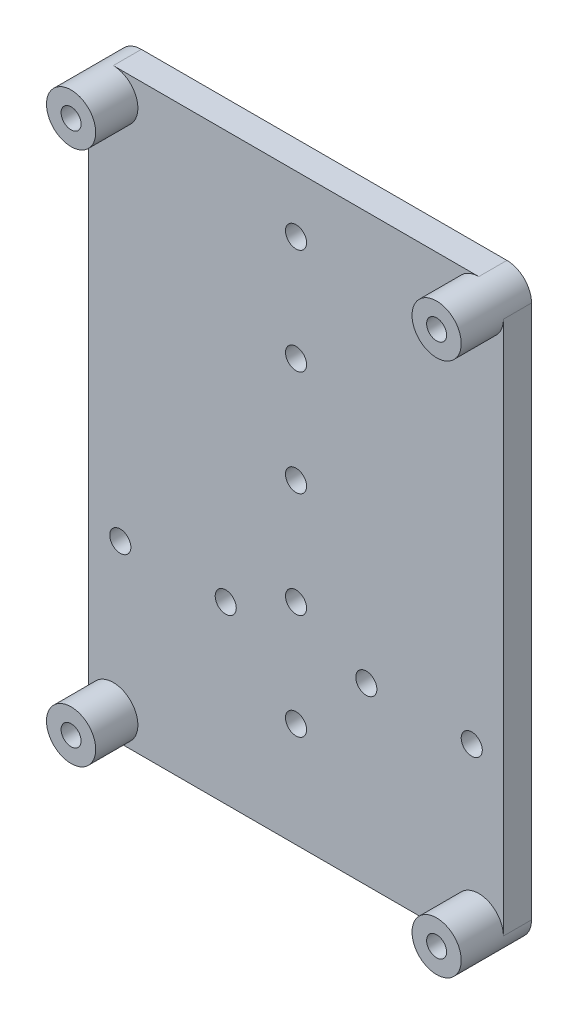
SolidWorks part; units mm, degrees
ref_plane "Front Plane" through (0, 0, 0) normal (0, 0, 1) x (1, 0, 0)
ref_plane "Top Plane" through (0, 0, 0) normal (0, 1, 0) x (1, 0, 0)
ref_plane "Right Plane" through (0, 0, 0) normal (1, 0, 0) x (0, 0, -1)
sketch "Sketch1" plane through (0, 0, 189.2667) normal (0, 0, 1) x (1, 0, 0)
  line L0 (108.5266, 109.7302) -> (160.5266, 109.7302) construction
  line L1 (164.0266, 113.2302) -> (164.0266, 189.2302) construction
  line L2 (105.0266, 189.2302) -> (105.0266, 113.2302) construction
  line L3 (160.5266, 192.7302) -> (108.5266, 192.7302) construction
  line L4 (108.5266, 109.7302) -> (160.5266, 109.7302)
  line L5 (164.0266, 113.2302) -> (164.0266, 189.2302)
  line L6 (105.0266, 189.2302) -> (105.0266, 113.2302)
  line L7 (160.5266, 192.7302) -> (108.5266, 192.7302)
  circle A0 centre (134.5266, 124.6371) radius 1.5 construction
  circle A1 centre (109.5266, 134.6371) radius 1.5 construction
  circle A2 centre (124.5266, 134.6371) radius 1.5 construction
  circle A3 centre (159.5266, 134.6371) radius 1.5 construction
  circle A4 centre (144.5266, 134.6371) radius 1.5 construction
  circle A5 centre (134.5266, 139.6371) radius 1.5 construction
  circle A6 centre (134.5266, 154.6371) radius 1.5 construction
  circle A7 centre (134.5266, 169.6371) radius 1.5 construction
  circle A8 centre (134.5266, 184.6371) radius 1.5 construction
  circle A9 centre (108.5266, 189.2302) radius 1.4224 construction
  circle A10 centre (160.5266, 189.2302) radius 1.4224 construction
  circle A11 centre (160.5266, 113.2302) radius 1.4224 construction
  circle A12 centre (108.5266, 113.2302) radius 1.4224 construction
  arc A13 (105.0266, 113.2302) -> (108.5266, 109.7302) centre (108.5266, 113.2302) ccw construction
  arc A14 (160.5266, 109.7302) -> (164.0266, 113.2302) centre (160.5266, 113.2302) ccw construction
  arc A15 (164.0266, 189.2302) -> (160.5266, 192.7302) centre (160.5266, 189.2302) ccw construction
  arc A16 (108.5266, 192.7302) -> (105.0266, 189.2302) centre (108.5266, 189.2302) ccw construction
  circle A17 centre (134.5266, 124.6371) radius 1.5
  circle A18 centre (109.5266, 134.6371) radius 1.5
  circle A19 centre (124.5266, 134.6371) radius 1.5
  circle A20 centre (159.5266, 134.6371) radius 1.5
  circle A21 centre (144.5266, 134.6371) radius 1.5
  circle A22 centre (134.5266, 139.6371) radius 1.5
  circle A23 centre (134.5266, 154.6371) radius 1.5
  circle A24 centre (134.5266, 169.6371) radius 1.5
  circle A25 centre (134.5266, 184.6371) radius 1.5
  circle A26 centre (108.5266, 189.2302) radius 1.4224
  circle A27 centre (160.5266, 189.2302) radius 1.4224
  circle A28 centre (160.5266, 113.2302) radius 1.4224
  circle A29 centre (108.5266, 113.2302) radius 1.4224
  arc A30 (105.0266, 113.2302) -> (108.5266, 109.7302) centre (108.5266, 113.2302) ccw
  arc A31 (160.5266, 109.7302) -> (164.0266, 113.2302) centre (160.5266, 113.2302) ccw
  arc A32 (164.0266, 189.2302) -> (160.5266, 192.7302) centre (160.5266, 189.2302) ccw
  arc A33 (108.5266, 192.7302) -> (105.0266, 189.2302) centre (108.5266, 189.2302) ccw
extrude "Boss-Extrude1" add sketch "Sketch1" along normal blind 4
sketch "Sketch2" plane through (0, 0, 193.2667) normal (0, 0, 1) x (1, 0, 0)
  circle A0 centre (108.5266, 189.2302) radius 1.4224
  circle A1 centre (108.5266, 189.2302) radius 3.5
  circle A2 centre (160.5266, 189.2302) radius 1.4224
  circle A3 centre (160.5266, 189.2302) radius 3.5
  circle A4 centre (108.5266, 113.2302) radius 1.4224
  circle A5 centre (108.5266, 113.2302) radius 3.5
  circle A6 centre (160.5266, 113.2302) radius 1.4224
  circle A7 centre (160.5266, 113.2302) radius 3.5
extrude "Boss-Extrude2" add sketch "Sketch2" along normal blind 6
